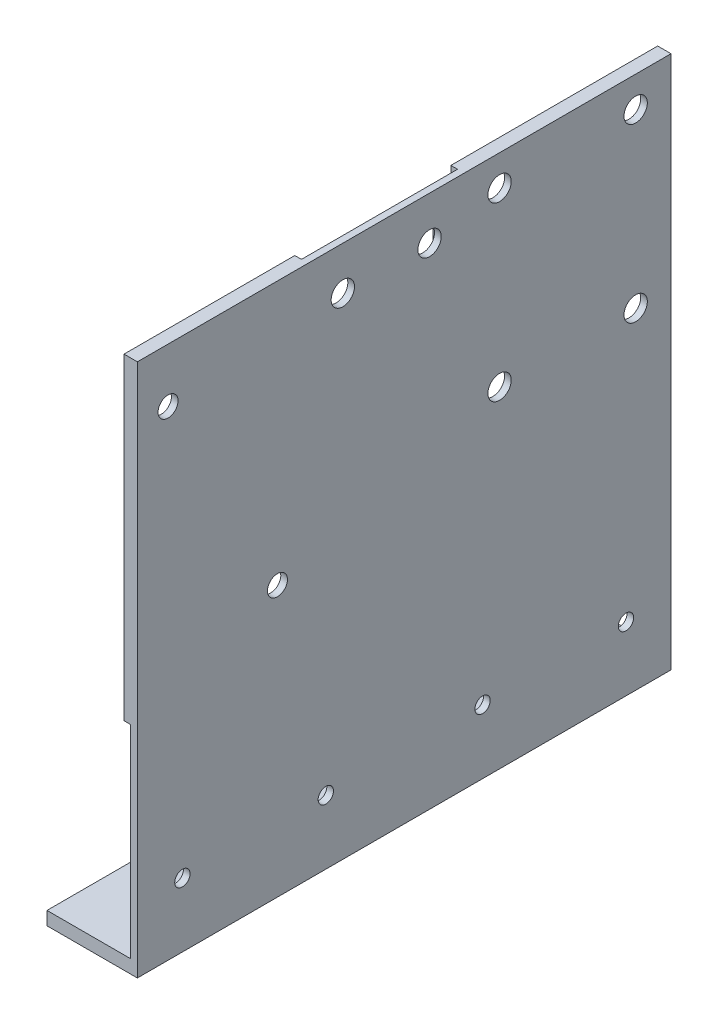
SolidWorks part; units mm, degrees
ref_plane "Front Plane" through (0, 0, 0) normal (0, 0, 1) x (1, 0, 0)
ref_plane "Top Plane" through (0, 0, 0) normal (0, 1, 0) x (1, 0, 0)
ref_plane "Right Plane" through (0, 0, 0) normal (1, 0, 0) x (0, 0, -1)
sketch "Sketch1" plane through (0, 0, 0) normal (0, 0, 1) x (1, 0, 0)
  line L0 (0, 0) -> (0, 2)
  line L3 (13.55, 0) -> (0, 0)
  line L4 (13.55, 0) -> (13.55, 80)
  line L5 (12.55, 80) -> (12.55, 2)
  line L8 (13.55, 80) -> (12.55, 80)
  line L9 (0, 2) -> (12.55, 2)
  point P3 (0, 0)
  point P8 (0, 0)
  point P9 (12.4205, 2)
  dimension "D1" = 2
  dimension "D2" = 80
  dimension "D3" = 12.55
  dimension "D6" = 1
extrude "Base" add sketch "Sketch1" along normal blind 80
sketch "Sketch3" plane through (0, 2, 0) normal (0, 1, 0) x (1, 0, 0)
  line L0 (6.275, 0) -> (6.275, -10) construction
  line L2 (6.275, -10) -> (6.275, -70) construction
  line L3 (6.275, -70) -> (6.275, -80) construction
  line L4 (12.55, 0) -> (0, 0) construction
  line L5 (12.55, -80) -> (0, -80) construction
  circle A0 centre (6.275, -10) radius 1.75
  circle A1 centre (6.275, -70) radius 1.75
  point P5 (0, 0)
  point P6 (0, 0)
  dimension "D1" = 3.5
  dimension "D2" = 3.5
  dimension "D3" = 10
extrude "Screw_Holes_Base" cut sketch "Sketch3" against normal up to next
sketch "Sketch6" plane through (12.55, -16.8717, -147.3131) normal (-1, 0, 0) x (0, 0, 1)
  line L0 (147.3131, 96.8717) -> (147.3131, 18.8717) construction
  line L1 (149.3131, 94.8717) -> (176.3131, 94.8717)
  line L2 (149.3131, 94.8717) -> (149.3131, 60.3717)
  line L3 (149.3131, 60.3717) -> (176.3131, 60.3717)
  line L4 (176.3131, 94.8717) -> (176.3131, 60.3717)
  line L6 (147.3131, 96.8717) -> (147.3131, 58.3717)
  line L7 (147.3131, 58.3717) -> (178.3131, 58.3717)
  line L8 (178.3131, 96.8717) -> (178.3131, 58.3717)
  line L9 (147.3131, 96.8717) -> (178.3131, 96.8717)
  line L11 (227.3131, 96.8717) -> (147.3131, 96.8717) construction
  dimension "D1" = 27
  dimension "D2" = 34.5
  dimension "D3" = 2
  dimension "D4" = 0
  dimension "D5" = 0
extrude "S2Mini" add sketch "Sketch6" along normal blind 1
sketch "Sketch8" plane through (12.55, 0, 13.55) normal (1, 0, 0) x (0, 0, -1)
  line L0 (8.25, 75.4) -> (-12.15, 75.4) construction
  line L1 (-12.15, 75.4) -> (-12.15, 49.6) construction
  line L2 (-12.15, 49.6) -> (8.25, 49.6) construction
  line L3 (8.25, 49.6) -> (8.25, 75.4) construction
  line L4 (-15.45, 78) -> (11.55, 78) construction
  line L6 (-12.15, 49.6) -> (-15.45, 49.6) construction
  line L7 (-15.45, 43.5) -> (-15.45, 78) construction
  line L8 (8.25, 49.6) -> (11.55, 49.6) construction
  line L9 (11.55, 78) -> (11.55, 43.5) construction
  circle A0 centre (-12.15, 75.4) radius 1.75
  circle A1 centre (8.25, 75.4) radius 1.75
  circle A2 centre (-12.15, 49.6) radius 1.75
  circle A3 centre (8.25, 49.6) radius 1.75
  dimension "D1" = 20.4
  dimension "D2" = 3.5
  dimension "D3" = 3.5
  dimension "D4" = 25.8
  dimension "D5" = 2.6
extrude "Screw_Holes_S2Mini" cut sketch "Sketch8" along normal blind 10
sketch "Sketch10" plane through (12.55, 37.1515, -62.267) normal (-1, 0, 0) x (0, 0, 1)
  line L0 (109.267, -8.6515) -> (109.267, -32.1515)
  line L1 (111.267, -10.6515) -> (138.267, -10.6515)
  line L2 (111.267, -10.6515) -> (111.267, -30.1515)
  line L3 (111.267, -30.1515) -> (138.267, -30.1515)
  line L4 (138.267, -10.6515) -> (138.267, -30.1515)
  line L5 (109.267, -32.1515) -> (140.267, -32.1515)
  line L6 (140.267, -8.6515) -> (140.267, -32.1515)
  line L7 (109.267, -8.6515) -> (140.267, -8.6515)
  line L14 (142.267, 42.8485) -> (142.267, -35.1515) construction
  line L15 (142.267, -35.1515) -> (62.267, -35.1515) construction
  dimension "D1" = 19.5
  dimension "D2" = 27
  dimension "D4" = 2
  dimension "D5" = 3
  dimension "D3" = 2
extrude "MD" add sketch "Sketch10" along normal blind 1
sketch "Sketch12" plane through (12.55, 0, 13.55) normal (1, 0, 0) x (0, 0, -1)
  line L0 (-59.7, 9.6) -> (-38.2, 9.6) construction
  line L1 (-48.95, 26.5) -> (-48.95, 7) construction
  line L2 (-62.45, 26.5) -> (-35.45, 26.5) construction
  line L3 (-35.45, 7) -> (-62.45, 7) construction
  circle A0 centre (-59.7, 9.6) radius 1.15
  circle A1 centre (-38.2, 9.6) radius 1.15
  point P10 (-48.95, 9.6)
  dimension "D1" = 21.5
  dimension "D2" = 2.3
  dimension "D3" = 2.3
  dimension "D4" = 2.6
extrude "Screw_Holes_MD" cut sketch "Sketch12" along normal blind 10
ref_plane "Plane1" through (0, 0, 40) normal (0, 0, 1) x (1, 0, 0)
mirror "Mirror1" about plane through (0, 0, 40) normal (0, 0, 1) of "Screw_Holes_MD", "MD"
sketch "Sketch14" plane through (12.55, 28.8323, -107.1539) normal (-1, 0, 0) x (0, 0, 1)
  line L0 (161.5539, 51.1677) -> (161.5539, 3.5677)
  line L1 (163.5539, 49.1677) -> (185.1539, 49.1677)
  line L2 (163.5539, 49.1677) -> (163.5539, 5.5677)
  line L3 (163.5539, 5.5677) -> (185.1539, 5.5677)
  line L4 (185.1539, 49.1677) -> (185.1539, 5.5677)
  line L5 (161.5539, 3.5677) -> (187.1539, 3.5677)
  line L6 (187.1539, 51.1677) -> (187.1539, 3.5677)
  line L7 (161.5539, 51.1677) -> (187.1539, 51.1677)
  line L8 (187.1539, 51.1677) -> (138.1539, 51.1677) construction
  line L13 (187.1539, 51.1677) -> (187.1539, -26.8323) construction
  dimension "D1" = 43.6
  dimension "D2" = 21.6
  dimension "D4" = 0
  dimension "D5" = 0
  dimension "D3" = 2
extrude "BC" add sketch "Sketch14" along normal blind 1
sketch "Sketch16" plane through (12.55, 0, 13.55) normal (1, 0, 0) x (0, 0, -1)
  line L4 (-64.45, 78) -> (-42.85, 78) construction
  line L5 (-64.45, 34.4) -> (-64.45, 78) construction
  line L6 (-42.85, 78) -> (-42.85, 34.4) construction
  line L7 (-42.85, 34.4) -> (-64.45, 34.4) construction
  circle A0 centre (-45.45, 40.5) radius 1.5
  circle A1 centre (-61.85, 71.9) radius 1.5
  point P2 (-43.865, 35.7548)
  point P8 (0, 0)
  point P9 (-56.8829, 68.1174)
  dimension "D1" = 2.6
  dimension "D2" = 3
  dimension "D4" = 3
  dimension "D3" = 6.1
  dimension "D5" = 6.1
  dimension "D6" = 2.6
extrude "Screw_Holes_BC" cut sketch "Sketch16" along normal blind 10
sketch "Sketch17" plane through (12.55, 0, 0) normal (-1, 0, 0) x (0, 0, 1)
  line L0 (52.7, 77) -> (52.7, 50)
  line L1 (33.7, 76) -> (51.7, 76)
  line L2 (33.7, 76) -> (33.7, 51)
  line L3 (33.7, 51) -> (51.7, 51)
  line L4 (51.7, 76) -> (51.7, 51)
  line L5 (32.7, 50) -> (52.7, 50)
  line L6 (32.7, 77) -> (32.7, 50)
  line L7 (32.7, 77) -> (52.7, 77)
  line L8 (54.4, 80) -> (31, 80) construction
  line L9 (31, 50) -> (54.4, 50) construction
  line L10 (31, 41.5) -> (31, 80) construction
  line L11 (54.4, 80) -> (54.4, 32.4) construction
  point P16 (42.7, 50)
  point P17 (42.7, 50)
  dimension "D1" = 25
  dimension "D2" = 18
  dimension "D4" = 3
  dimension "D3" = 1
extrude "LA" add sketch "Sketch17" along normal blind 1
sketch "Sketch18" plane through (12.55, 0, 0) normal (-1, 0, 0) x (0, 0, 1)
  line L0 (51.7, 76) -> (33.7, 76) construction
  line L2 (33.7, 76) -> (33.7, 51) construction
  line L3 (51.7, 51) -> (51.7, 76) construction
  line L4 (51.7, 76) -> (33.7, 76) construction
  circle A0 centre (36.2, 73.5) radius 1.75
  circle A1 centre (49.2, 73.5) radius 1.75
  dimension "D1" = 3.5
  dimension "D2" = 2.5
  dimension "D3" = 2.5
  dimension "D4" = 2.5
  dimension "D5" = 2.5
extrude "Cut-Extrude6" cut sketch "Sketch18" against normal up to next
